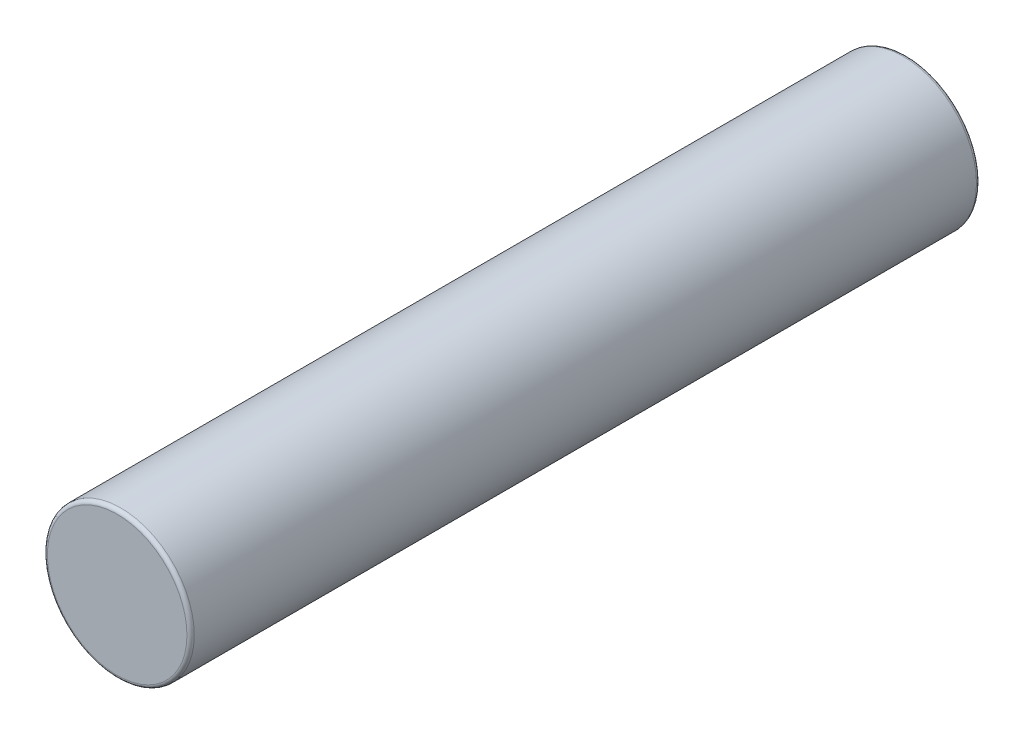
SolidWorks part; units mm, degrees
ref_plane "Front Plane" through (0, 0, 0) normal (0, 0, 1) x (1, 0, 0)
ref_plane "Top Plane" through (0, 0, 0) normal (0, 1, 0) x (1, 0, 0)
ref_plane "Right Plane" through (0, 0, 0) normal (1, 0, 0) x (0, 0, -1)
sketch "Sketch1" plane through (0, 0, 0) normal (0, 0, 1) x (1, 0, 0)
  circle A1 centre (0, 0) radius 2
  dimension "D1" = 4
extrude "Boss-Extrude1" add sketch "Sketch1" along normal blind 21.5
fillet "Fillet1" radius 0.1 2 edges at (2, 0, 21.5) (2, 0, 0)
